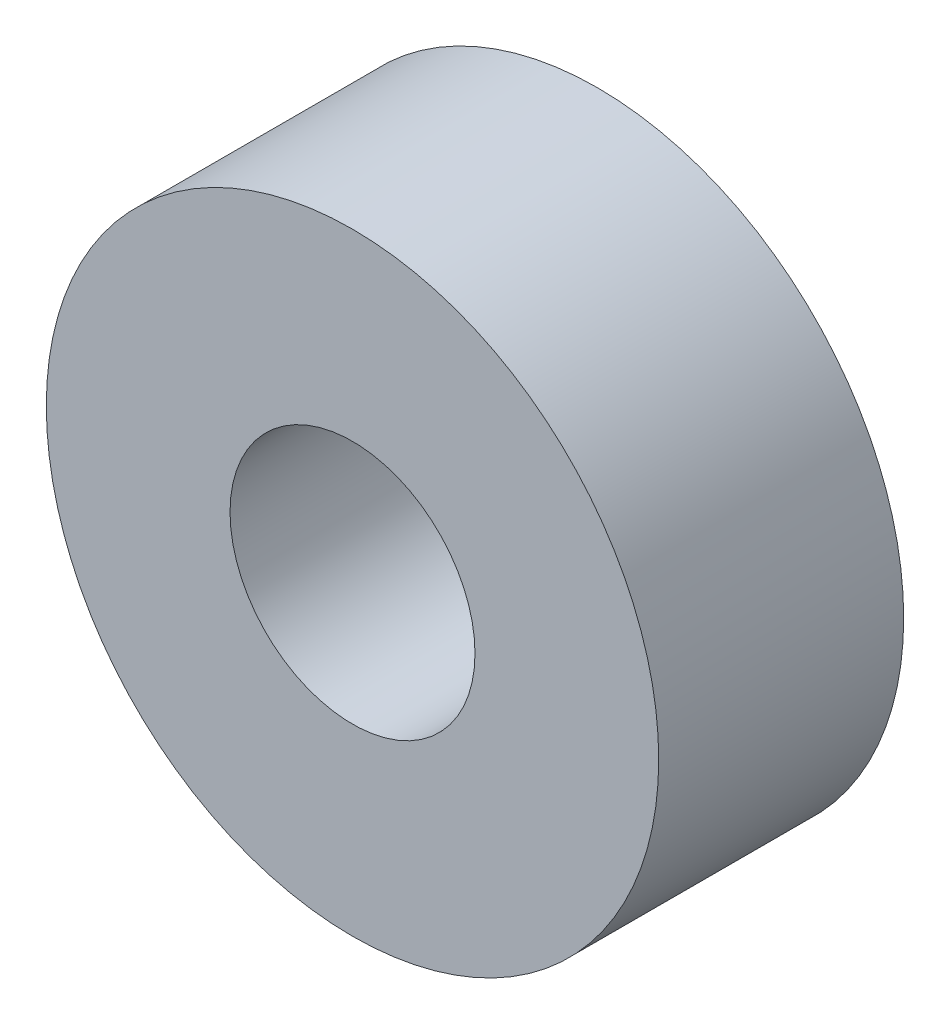
SolidWorks part; units mm, degrees
ref_plane "前视基准面" through (0, 0, 0) normal (0, 0, 1) x (1, 0, 0)
ref_plane "上视基准面" through (0, 0, 0) normal (0, 1, 0) x (1, 0, 0)
ref_plane "右视基准面" through (0, 0, 0) normal (1, 0, 0) x (0, 0, -1)
sketch "草图1" plane through (0, 0, 0) normal (0, 0, 1) x (1, 0, 0)
  circle A0 centre (-11.8371, 28.2476) radius 5
  dimension "D1" = 10
extrude "凸台-拉伸1" add sketch "草图1" along normal blind 4 contours A0
sketch "草图2" plane through (0, 0, 4) normal (0, 0, 1) x (1, 0, 0)
  circle A0 centre (-11.8371, 28.2476) radius 2
  dimension "D1" = 4
extrude "切除-拉伸1" cut sketch "草图2" against normal through all
